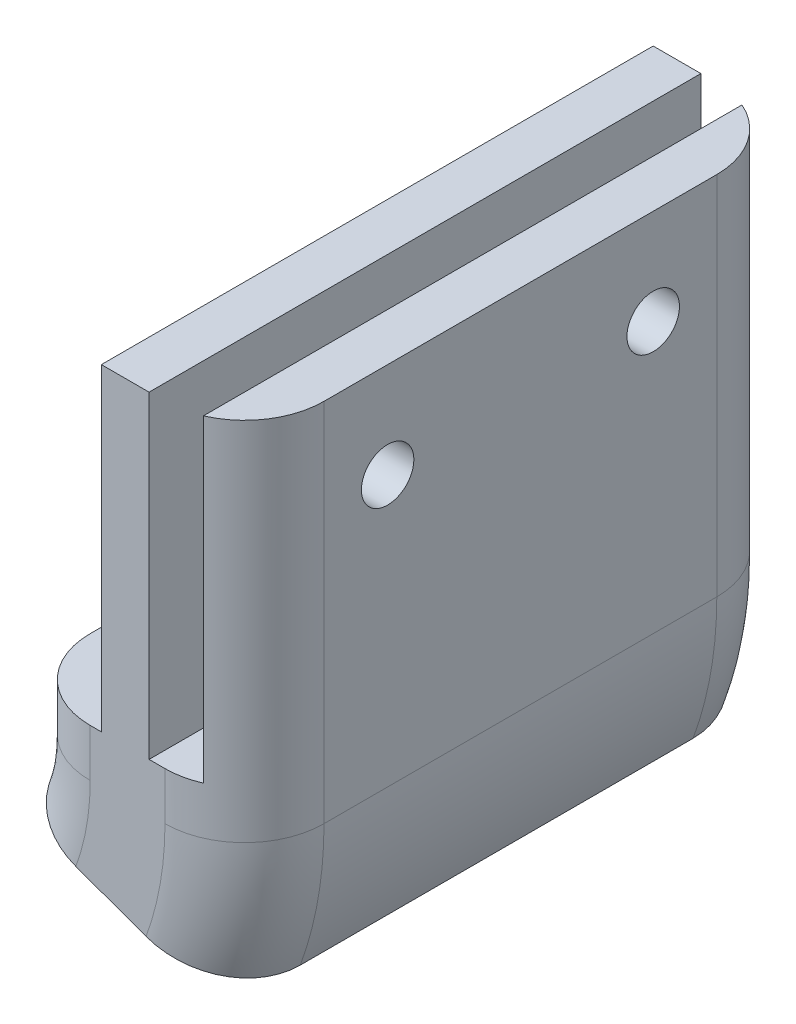
SolidWorks part; units mm, degrees
ref_plane "Plan de face" through (0, 0, 0) normal (0, 0, 1) x (1, 0, 0)
ref_plane "Plan de dessus" through (0, 0, 0) normal (0, 1, 0) x (1, 0, 0)
ref_plane "Plan de droite" through (0, 0, 0) normal (1, 0, 0) x (0, 0, -1)
sketch "Esquisse1" plane through (0, 0, 0) normal (0, 1, 0) x (1, 0, 0)
  line L5 (2.35, -17.35) -> (-2.35, -17.35)
  line L6 (7.35, -12.35) -> (7.35, 12.35)
  line L7 (2.35, 17.35) -> (-2.35, 17.35)
  line L8 (-7.35, -12.35) -> (-7.35, 12.35)
  line L9 (7.35, -17.35) -> (-7.35, 17.35) construction
  line L10 (7.35, 17.35) -> (-7.35, -17.35) construction
  arc A0 (2.35, -17.35) -> (7.35, -12.35) centre (2.35, -12.35) ccw
  arc A1 (-2.35, -17.35) -> (-7.35, -12.35) centre (-2.35, -12.35) cw
  arc A2 (-2.35, 17.35) -> (-7.35, 12.35) centre (-2.35, 12.35) ccw
  arc A3 (7.35, 12.35) -> (2.35, 17.35) centre (2.35, 12.35) ccw
  point P0 (0, 0)
  dimension "D3" = 5
  dimension "D1" = 14.7
  dimension "D2" = 34.7
extrude "Boss.-Extru.1" add sketch "Esquisse1" along normal blind 3
sketch "Esquisse4" plane through (0, 0, 0) normal (0, -1, 0) x (1, 0, 0)
  line L0 (2.35, -17.35) -> (-2.35, -17.35)
  line L1 (7.35, -12.35) -> (7.35, 12.35)
  line L2 (2.35, 17.35) -> (-2.35, 17.35)
  line L3 (-7.35, -12.35) -> (-7.35, 12.35)
  line L4 (7.35, -17.35) -> (-7.35, 17.35) construction
  line L5 (7.35, 17.35) -> (-7.35, -17.35) construction
  line L6 (-17.35, 12.35) -> (-17.35, -11.9197) construction
  arc A0 (2.35, -17.35) -> (7.35, -12.35) centre (2.35, -12.35) ccw
  arc A1 (-2.35, -17.35) -> (-7.35, -12.35) centre (-2.35, -12.35) cw
  arc A2 (-2.35, 17.35) -> (-7.35, 12.35) centre (-2.35, 12.35) ccw
  arc A3 (7.35, 12.35) -> (2.35, 17.35) centre (2.35, 12.35) ccw
  point P0 (0, 0)
  dimension "D3" = 5
  dimension "D1" = 14.7
  dimension "D2" = 34.7
  dimension "D4" = 10
revolve "Révolution1" add sketch "Esquisse4" angle 20 about L6
sketch "Esquisse5" plane through (0, 3, 0) normal (0, 1, 0) x (1, 0, 0)
  line L8 (1.35, -17.35) -> (-1.65, -17.35)
  line L28 (7.35, -12.35) -> (7.35, 12.35)
  line L29 (1.35, 17.35) -> (-1.65, 17.35)
  line L31 (7.35, -17.35) -> (6.4464, -15.217) construction
  line L33 (4.35, 16.9326) -> (4.35, -16.9326)
  line L34 (1.35, 17.35) -> (1.35, -17.35)
  line L35 (-1.65, 17.35) -> (-1.65, -17.35)
  arc A2 (4.35, -16.9326) -> (7.35, -12.35) centre (2.35, -12.35) ccw
  arc A5 (7.35, 12.35) -> (4.35, 16.9326) centre (2.35, 12.35) ccw
  point P0 (0, 0)
  dimension "D3" = 5
  dimension "D4" = 3
  dimension "D5" = 3
  dimension "D6" = 3
extrude "Boss.-Extru.2" add sketch "Esquisse5" along normal blind 20
sketch "Esquisse6" plane through (7.35, 0, 0) normal (1, 0, 0) x (0, 0, -1)
  line L2 (0, 23) -> (0, 18.0447) construction
  line L3 (-12.35, 23) -> (12.35, 23) construction
  line L4 (-12.35, 23) -> (-12.35, 0) construction
  circle A0 centre (-8.35, 17) radius 1.65
  circle A1 centre (8.35, 17) radius 1.65
  point P12 (0, 23)
  dimension "D1" = 3.3
  dimension "D2" = 6
  dimension "D3" = 4
extrude "Enlèv. mat.-Extru.1" cut sketch "Esquisse6" against normal through all
sketch "Esquisse8" plane through (-1.65, 0, 0) normal (-1, 0, 0) x (0, 0, 1)
  line L0 (-6.7046, 19.85) -> (-9.9954, 19.85)
  line L1 (-9.9954, 19.85) -> (-11.6409, 17)
  line L2 (-11.6409, 17) -> (-9.9954, 14.15)
  line L3 (-9.9954, 14.15) -> (-6.7046, 14.15)
  line L4 (-6.7046, 14.15) -> (-5.0591, 17)
  line L5 (-5.0591, 17) -> (-6.7046, 19.85)
  line L6 (-11.6409, 17) -> (-5.0591, 17) construction
  line L7 (9.9954, 19.85) -> (6.7046, 19.85)
  line L8 (6.7046, 19.85) -> (5.0591, 17)
  line L9 (5.0591, 17) -> (6.7046, 14.15)
  line L10 (6.7046, 14.15) -> (9.9954, 14.15)
  line L11 (9.9954, 14.15) -> (11.6409, 17)
  line L12 (11.6409, 17) -> (9.9954, 19.85)
  line L13 (5.0591, 17) -> (11.6409, 17) construction
  circle A0 centre (-8.35, 17) radius 1.65 construction
  circle A1 centre (8.35, 17) radius 1.65 construction
  point P0 (-8.35, 17)
  point P1 (8.35, 17)
  point P5 (-8.35, 14.15)
  point P9 (-8.35, 17)
  point P10 (-8.35, 17)
  point P14 (8.35, 14.15)
  point P18 (8.35, 17)
  point P19 (8.35, 17)
  dimension "D1" = 5.7
  dimension "D2" = 120
  dimension "D3" = 5.7
  dimension "D4" = 5.7
  dimension "D5" = 120
  dimension "D6" = 5.7
extrude "Enlèv. mat.-Extru.3" cut sketch "Esquisse8" against normal up to next
